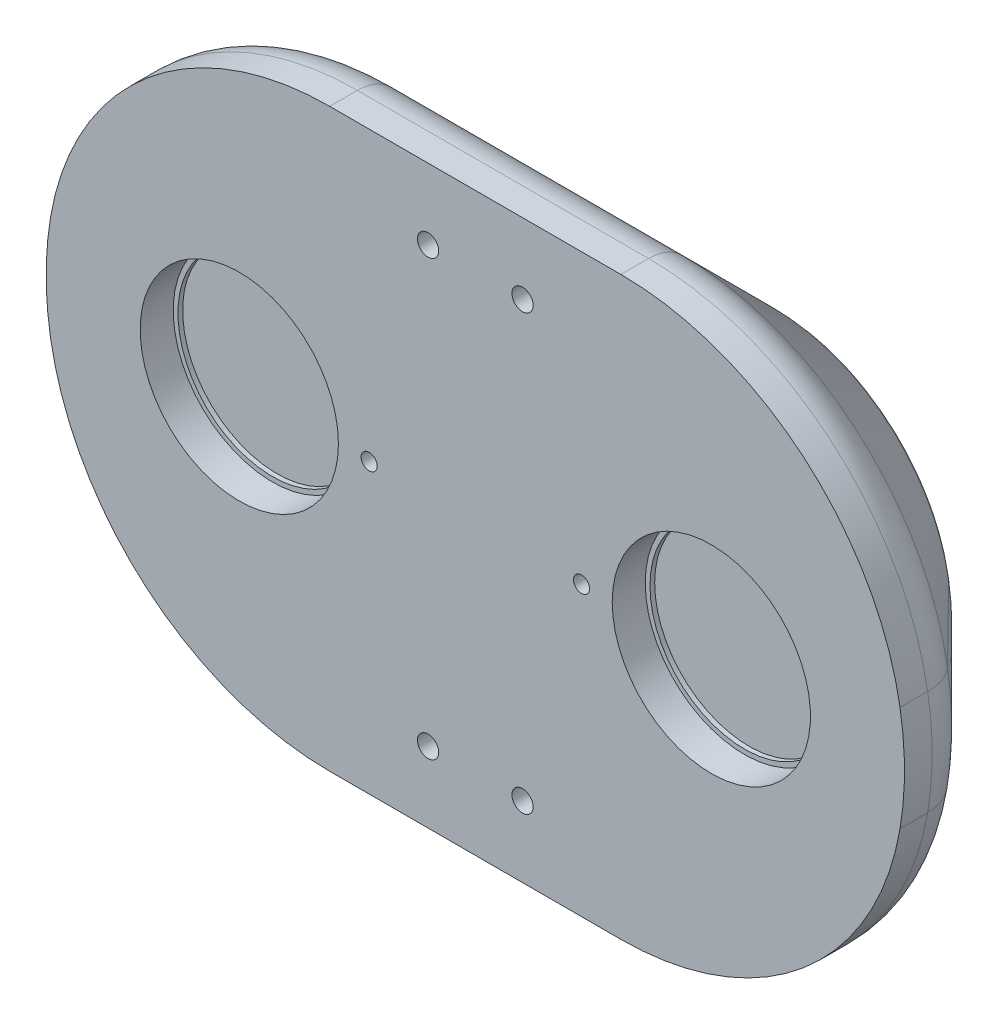
SolidWorks part; units mm, degrees
material "ABS"
ref_plane "Front" through (0, 0, 0) normal (0, 0, 1) x (1, 0, 0)
ref_plane "Top" through (0, 0, 0) normal (0, 1, 0) x (1, 0, 0)
ref_plane "Right" through (0, 0, 0) normal (1, 0, 0) x (0, 0, -1)
sketch "ｽｹｯﾁ1" plane through (0, 0, 0) normal (0, 0, 1) x (1, 0, 0)
  line L0 (-25, 0) -> (0, 0) construction
  line L3 (-50, 61) -> (50, 61)
  line L4 (-50, 61) -> (-50, -61) construction
  line L5 (-50, -61) -> (50, -61)
  line L6 (50, 61) -> (50, -61) construction
  line L7 (-50, 61) -> (50, -61) construction
  line L8 (-50, -61) -> (50, 61) construction
  line L9 (0, 0) -> (25, 0) construction
  arc A2 (-50, 61) -> (-50, -61) centre (-25, 0) ccw
  arc A3 (50, 61) -> (50, -61) centre (25, 0) cw
  point P0 (0, 0)
  point P8 (-90.9242, 0)
  point P9 (90.9242, 0)
  point P11 (68.8001, 0)
  dimension "D2" = 122
  dimension "D1" = 100
  dimension "D3" = 50
extrude "ﾎﾞｽ - 押し出し1" add sketch "ｽｹｯﾁ1" along normal blind 35
fillet "ﾌｨﾚｯﾄ1" radius 60 4 edges at (50, -61, 17.5) (-50, -61, 17.5) (50, 61, 17.5) (-50, 61, 17.5)
sketch "ｽｹｯﾁ3" plane through (0, 0, 35) normal (0, 0, 1) x (1, 0, 0)
  line L0 (-50, 0) -> (50, 0) construction
  circle A0 centre (-50, 0) radius 21
  point P4 (0, 0)
  dimension "D1" = 42
  dimension "D2" = 100
extrude "ｶｯﾄ - 押し出し1" cut sketch "ｽｹｯﾁ3" against normal blind 7
sketch "ｽｹｯﾁ4" plane through (0, 0, 28) normal (0, 0, 1) x (1, 0, 0)
  circle A0 centre (-50, 0) radius 20
  circle A1 centre (-50, 0) radius 21 construction
  dimension "D1" = 1
extrude "ｶｯﾄ - 押し出し2" cut sketch "ｽｹｯﾁ4" against normal blind 1
mirror "ﾐﾗｰ1" about plane through (0, 0, 0) normal (1, 0, 0) of "ｶｯﾄ - 押し出し2", "ｶｯﾄ - 押し出し1"
chamfer "面取り1" distance 25 angle 45 8 edges at (-69.5194, -46.8676, 0) (-90.9242, 0, 0) (0, -61, 0) (-69.5194, 46.8676, 0) (69.5194, -46.8676, 0) (0, 61, 0) (90.9242, 0, 0) (69.5194, 46.8676, 0)
fillet "ﾌｨﾚｯﾄ3" radius 10 16 edges at (0, 36, 0) (-53.4027, 27.7561, 0) (-65.9242, 0, 0) (-53.4027, -27.7561, 0) (0, -36, 0) (53.4027, -27.7561, 0) (65.9242, 0, 0) (90.9242, 0, 25) (69.5194, -46.8676, 25) (0, -61, 25) (-69.5194, -46.8676, 25) (-90.9242, 0, 25) (-69.5194, 46.8676, 25) (0, 61, 25) (53.4027, 27.7561, 0) (69.5194, 46.8676, 25)
sketch "ｽｹｯﾁ5" plane through (0, 0, 0) normal (0, 0, -1) x (-1, 0, 0)
  text T0 "TRUST DOG" font "Cooper Black" height in points 36
  point P1 (0, 0)
extrude "ｶｯﾄ - 押し出し3" cut sketch "ｽｹｯﾁ5" against normal blind 0.5
sketch "ｽｹｯﾁ6" plane through (0, 0, 0) normal (0, 0, -1) x (-1, 0, 0)
  line L0 (-32.5, 0) -> (32.5, 0) construction
  line L1 (-32.5, 12.5) -> (32.5, 12.5)
  line L2 (-32.5, -12.5) -> (32.5, -12.5)
  arc A0 (-32.5, 12.5) -> (-32.5, -12.5) centre (-32.5, 0) ccw
  arc A1 (32.5, -12.5) -> (32.5, 12.5) centre (32.5, 0) ccw
  point P2 (0, 0)
  dimension "D2" = 12.5
  dimension "D1" = 65
extrude "ｶｯﾄ - 押し出し4" cut sketch "ｽｹｯﾁ6" against normal blind 25
hole_wizard "M3 すきま穴1" positions "ｽｹｯﾁ7" profile "ｽｹｯﾁ8" hole size "M3" standard "JIS" end condition through all
sketch "ｽｹｯﾁ7" plane through (0, 0, 25) normal (0, 0, -1) x (-1, 0, 0)
  line L0 (0, 0) -> (-22.5, 0) construction
  line L3 (0, 0) -> (22.5, 0) construction
  line L6 (0, 61) -> (0, -61) construction
  line L7 (-30.8392, 61) -> (30.8392, 61) construction
  line L8 (30.8392, -61) -> (-30.8392, -61) construction
  point P2 (-22.5, 0)
  point P9 (22.5, 0)
  point P28 (0, 0)
  dimension "D1" = 45
sketch "ｽｹｯﾁ8" plane through (-22.5, 0, 25) normal (1, 0, 0) x (0, 1, 0)
  line L0 (0, 0) -> (0, 10)
  line L1 (0, 10) -> (1.7, 10)
  line L2 (1.7, 10) -> (1.7, 0)
  line L5 (1.7, 0) -> (0, 0)
  line L11 (0, -6.35) -> (0, 107.95) construction
  dimension "通し穴の直径" = 3.4
  dimension "通し穴の深さ" = 10
hole_wizard "M4 穴付きねじ用座ぐり穴1" positions "ｽｹｯﾁ10" profile "ｽｹｯﾁ11" counterbore size "M4" standard "JIS" end condition through all
sketch "ｽｹｯﾁ10" plane through (0, 0, 0) normal (0, 0, -1) x (-1, 0, 0)
  line L0 (-10, 46) -> (10, 46) construction
  line L3 (0, 46) -> (0, 0) construction
  line L5 (-30.8392, 61) -> (30.8392, 61) construction
  point P0 (-10, 46)
  point P2 (10, 46)
  dimension "D1" = 20
  dimension "D2" = 15
sketch "ｽｹｯﾁ11" plane through (10, 46, 0) normal (1, 0, 0) x (0, 1, 0)
  line L0 (0, 0) -> (0, 35)
  line L1 (0, 35) -> (2.25, 35)
  line L3 (2.25, 35) -> (2.25, 24)
  line L4 (2.25, 24) -> (4, 24)
  line L5 (4, 24) -> (4, 0)
  line L7 (4, 0) -> (0, 0)
  line L11 (0, -6.35) -> (0, 107.95) construction
  dimension "通し穴の直径" = 4.5
  dimension "通し穴の深さ" = 35
  dimension "座ぐり穴の直径" = 8
  dimension "座ぐり穴の深さ" = 24
mirror "ﾐﾗｰ2" about plane through (0, 0, 0) normal (0, 1, 0) of "M4 穴付きねじ用座ぐり穴1"
